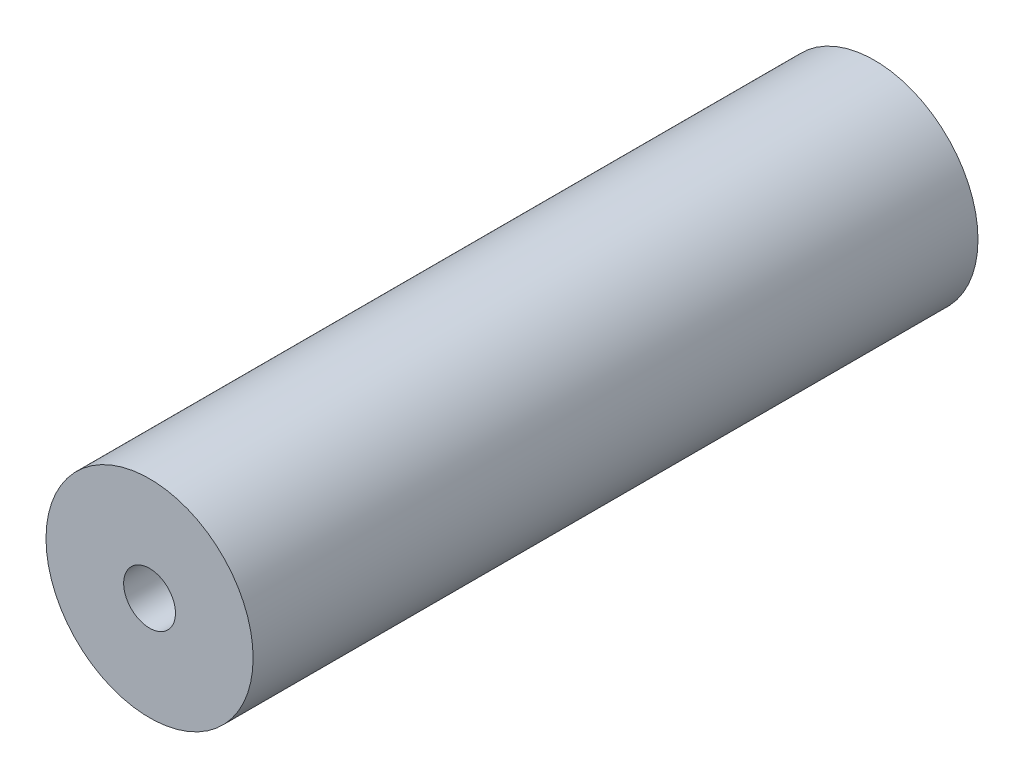
SolidWorks part; units mm, degrees
material "POLYURETHANE (11671)"
ref_plane "Front Plane" through (0, 0, 0) normal (0, 0, 1) x (1, 0, 0)
ref_plane "Top Plane" through (0, 0, 0) normal (0, 1, 0) x (1, 0, 0)
ref_plane "Right Plane" through (0, 0, 0) normal (1, 0, 0) x (0, 0, -1)
sketch "Sketch1" plane through (0, 0, 0) normal (0, 0, 1) x (1, 0, 0)
  circle A0 centre (0, 0) radius 25.4
  circle A1 centre (0, 0) radius 6.35
  dimension "D1" = 50.8
  dimension "D2" = 12.7
extrude "Boss-Extrude1" add sketch "Sketch1" along normal blind 177.8
